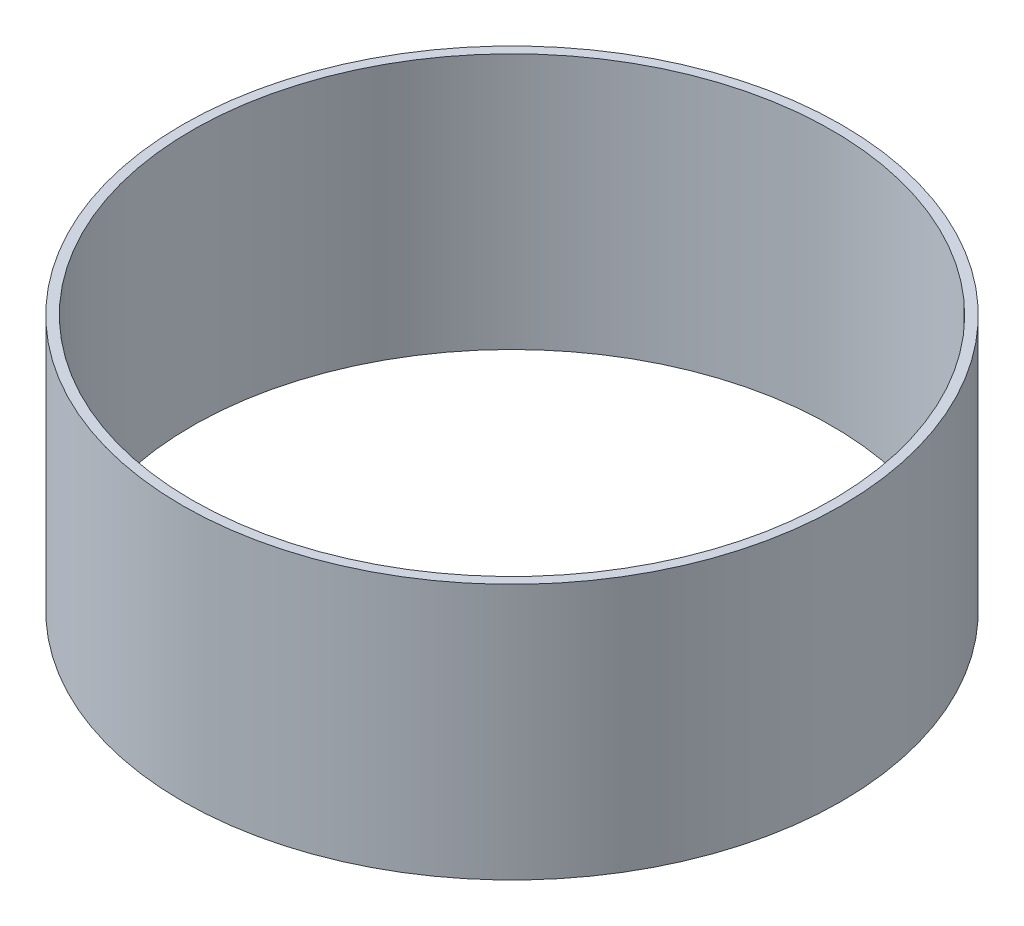
SolidWorks part; units mm, degrees
ref_plane "Front Plane" through (0, 0, 0) normal (0, 0, 1) x (1, 0, 0)
ref_plane "Top Plane" through (0, 0, 0) normal (0, 1, 0) x (1, 0, 0)
ref_plane "Right Plane" through (0, 0, 0) normal (1, 0, 0) x (0, 0, -1)
sketch "Sketch1" plane through (0, 0, 0) normal (0, 1, 0) x (1, 0, 0)
  circle A0 centre (0, 0) radius 65.405
  circle A1 centre (0, 0) radius 63.5
  dimension "D1" = 130.81
  dimension "D2" = 127
extrude "Boss-Extrude2" add sketch "Sketch1" along normal mid plane 50.8
